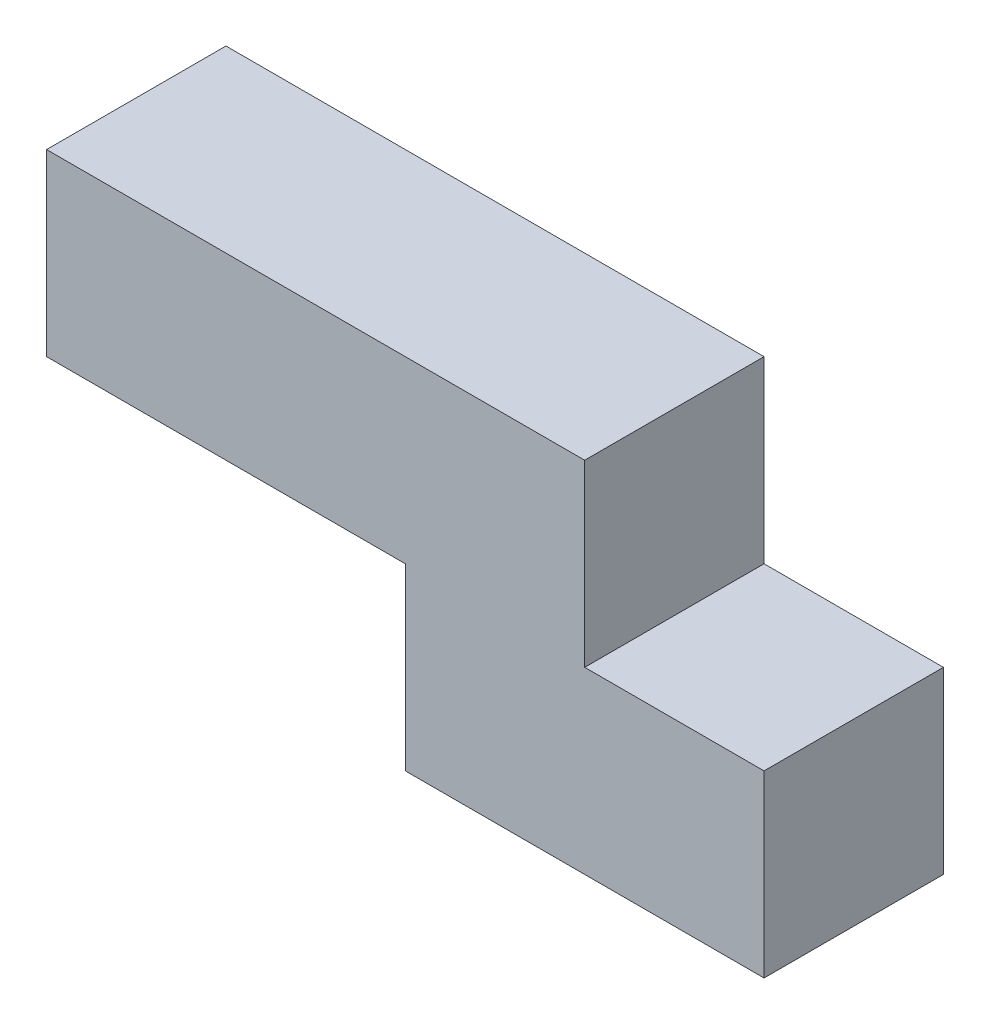
SolidWorks part; units mm, degrees
ref_plane "Front Plane" through (0, 0, 0) normal (0, 0, 1) x (1, 0, 0)
ref_plane "Top Plane" through (0, 0, 0) normal (0, 1, 0) x (1, 0, 0)
ref_plane "Right Plane" through (0, 0, 0) normal (1, 0, 0) x (0, 0, -1)
sketch "Sketch1" plane through (0, 0, 0) normal (0, 0, 1) x (1, 0, 0)
  line L36 (101.6, 0) -> (101.6, 25.4)
  line L37 (101.6, 25.4) -> (76.2, 25.4)
  line L38 (76.2, 25.4) -> (76.2, 50.8)
  line L39 (76.2, 50.8) -> (0, 50.8)
  line L40 (0, 50.8) -> (0, 25.4)
  line L41 (0, 25.4) -> (50.8, 25.4)
  line L42 (50.8, 25.4) -> (50.8, 0)
  line L43 (50.8, 0) -> (101.6, 0)
extrude "Boss-Extrude1" add sketch "Sketch1" along normal blind 25.4
